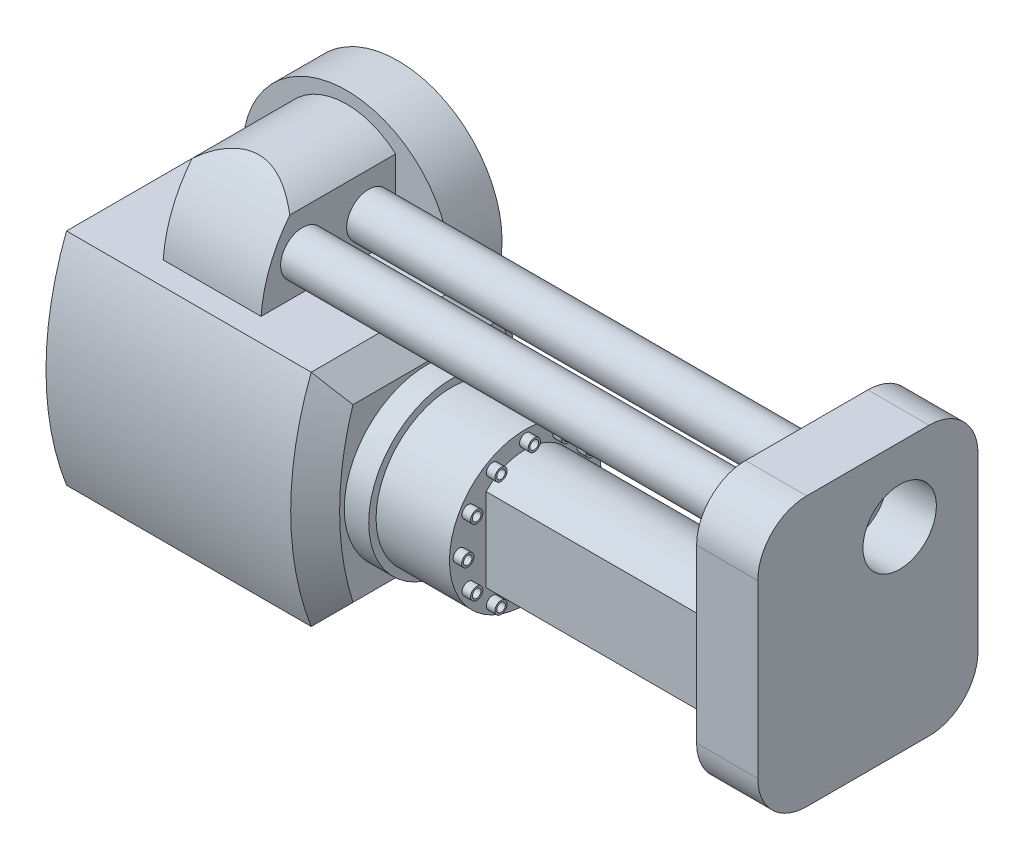
SolidWorks part; units mm, degrees
ref_plane "Front Plane" through (0, 0, 0) normal (0, 0, 1) x (1, 0, 0)
ref_plane "Top Plane" through (0, 0, 0) normal (0, 1, 0) x (1, 0, 0)
ref_plane "Right Plane" through (0, 0, 0) normal (1, 0, 0) x (0, 0, -1)
sketch "Sketch1" plane through (0, 0, 0) normal (1, 0, 0) x (0, 0, -1)
  line L0 (0, 49.4319) -> (0, -79.2344) construction
  line L1 (-101.7614, 0) -> (111.7272, 0) construction
  line L2 (-37.5, 45) -> (37.5, 45)
  line L3 (-37.5, -45) -> (37.5, -45)
  arc A0 (37.5, 45) -> (37.5, -45) centre (-79.119, 0) cw
  arc A1 (-37.5, 45) -> (-37.5, -45) centre (79.119, 0) ccw
  point P7 (0, 45)
  point P13 (0, -45)
  dimension "D3" = 125
  dimension "D1" = 37.5
  dimension "D2" = 37.5
  dimension "D4" = 45
extrude "Boss-Extrude1" add sketch "Sketch1" along normal blind 100
sketch "Sketch2" plane through (100, 0, 0) normal (1, 0, 0) x (0, 0, -1)
  line L2 (37.5, 45) -> (-37.5, 45)
  line L3 (-37.5, -45) -> (37.5, -45)
  line L4 (37.5, 45) -> (-37.5, 45)
  line L5 (-37.5, -45) -> (37.5, -45)
  arc A2 (37.5, -45) -> (37.5, 45) centre (-79.119, 0) ccw
  arc A3 (-37.5, 45) -> (-37.5, -45) centre (79.119, 0) ccw
  arc A4 (37.5, -45) -> (37.5, 45) centre (-79.119, 0) ccw
  arc A5 (-37.5, 45) -> (-37.5, -45) centre (79.119, 0) ccw
  dimension "D1" = 0
extrude "Boss-Extrude2" add sketch "Sketch2" along normal blind 10 draft 45
sketch "Sketch3" plane through (110, 0, 0) normal (1, 0, 0) x (0, 0, -1)
  circle A0 centre (0, 0) radius 34
  dimension "D1" = 68
extrude "Boss-Extrude3" add sketch "Sketch3" along normal blind 10
sketch "Sketch4" plane through (120, 0, 0) normal (1, 0, 0) x (0, 0, -1)
  circle A0 centre (0, 0) radius 31
  dimension "D1" = 62
extrude "Boss-Extrude4" add sketch "Sketch4" along normal blind 30
sketch "Sketch5" plane through (150, 0, 0) normal (1, 0, 0) x (0, 0, -1)
  line L0 (0, 0) -> (27, 0) construction
  circle A0 centre (27, 0) radius 2.5
  circle A1 centre (27, 0) radius 1.75
  circle A2 centre (0, 0) radius 31
  circle A3 centre (0, 0) radius 31
  dimension "D3" = 5
  dimension "D4" = 3.5
  dimension "D2" = 27
  dimension "D1" = 0
extrude "Boss-Extrude5" add sketch "Sketch5" along normal blind 3.5 contours A1 | A0
pattern_circular "CirPattern1" count 12 over 360 about axis through (0, 0, 0.1767) along (1, 0, 0) of "Boss-Extrude5"
sketch "Sketch6" plane through (150, 0, 0) normal (1, 0, 0) x (0, 0, -1)
  line L0 (-17.9184, 0) -> (19.6119, 0) construction
  line L1 (0, -13.9961) -> (0, 16.7727) construction
  line L2 (16, 0) -> (16, 17)
  line L3 (16, 0) -> (16, -17)
  line L4 (-16, 0) -> (-16, 17)
  line L5 (-16, 0) -> (-16, -17)
  arc A2 (-16, 17) -> (16, 17) centre (0, 1.9003) cw
  arc A3 (-16, -17) -> (16, -17) centre (0, -1.9003) ccw
  dimension "D5" = 22
  dimension "D6" = 22
  dimension "D1" = 17
  dimension "D2" = 17
  dimension "D3" = 17
  dimension "D4" = 17
  dimension "D7" = 16
  dimension "D8" = 16
  dimension "D9" = 16
  dimension "D10" = 16
  dimension "D11" = 16
extrude "Boss-Extrude6" add sketch "Sketch6" along normal blind 100
ref_plane "Plane1" through (0, 0, 37.5) normal (0, 0, 1) x (1, 0, 0)
sketch "Sketch10" plane through (0, 0, 37.5) normal (0, 0, 1) x (1, 0, 0)
  line L0 (100, -45) -> (0, -45) construction
  circle A0 centre (50, -45) radius 42.5
  dimension "D1" = 85
extrude "Boss-Extrude10" add sketch "Sketch10" along normal mid plane 21
sketch "Sketch11" plane through (0, 0, 27) normal (0, 0, -1) x (-1, 0, 0)
  line L0 (-50, -45) -> (-70, -45)
  line L1 (-100, -45) -> (0, -45) construction
  line L2 (-70, -45) -> (-70, -75)
  line L3 (-50, -45) -> (-30, -45)
  line L4 (-7.5, -45) -> (-92.5, -45) construction
  line L5 (-30, -45) -> (-30, -75)
  arc A0 (-70, -75) -> (-30, -75) centre (-50, -52.6393) ccw
  dimension "D5" = 30
  dimension "D1" = 20
  dimension "D2" = 20
  dimension "D3" = 30
  dimension "D4" = 30
extrude "Boss-Extrude11" add sketch "Sketch11" along normal blind 30
sketch "Sketch12" plane through (70, 0, 0) normal (1, 0, 0) x (0, 0, -1)
  line L0 (3, -45) -> (3, -87)
  line L1 (3, -45) -> (28, -45)
  line L2 (-37.5, -45) -> (37.5, -45) construction
  arc A0 (28, -45) -> (3, -87) centre (-26.8393, -40.7981) cw
  dimension "D3" = 55
  dimension "D1" = 42
  dimension "D2" = 25
extrude "Boss-Extrude12" add sketch "Sketch12" against normal blind 40
sketch "Sketch13" plane through (0, 0, -3) normal (0, 0, 1) x (1, 0, 0)
  line L3 (30, -75) -> (30, -87)
  line L4 (30, -87) -> (70, -87)
  line L5 (70, -87) -> (70, -75)
  line L6 (30, -75) -> (30, -87)
  line L7 (30, -87) -> (70, -87)
  line L8 (70, -87) -> (70, -75)
  arc A1 (30, -75) -> (70, -75) centre (50, -52.6393) ccw
  arc A2 (30, -75) -> (70, -75) centre (50, -52.6393) ccw
  dimension "D1" = 0
extrude "Cut-Extrude1" cut sketch "Sketch13" against normal blind 40
sketch "Sketch14" plane through (250, 0, 0) normal (1, 0, 0) x (0, 0, -1)
  line L0 (0, 0) -> (-110.3241, 0) construction
  line L2 (-40, 35) -> (10, 35)
  line L3 (-60, 15) -> (-60, -55)
  line L4 (-40, -75) -> (10, -75)
  line L5 (30, 15) -> (30, -55)
  line L6 (-60, 35) -> (30, -75) construction
  line L7 (-60, -75) -> (30, 35) construction
  circle A0 centre (-28, -45) radius 15
  arc A1 (10, -75) -> (30, -55) centre (10, -55) ccw
  arc A2 (30, 15) -> (10, 35) centre (10, 15) ccw
  arc A3 (-40, 35) -> (-60, 15) centre (-40, 15) ccw
  arc A4 (-40, -75) -> (-60, -55) centre (-40, -55) cw
  point P5 (-15, -20)
  point P22 (-54.1421, -69.1421)
  dimension "D1" = 30
  dimension "D8" = 20
  dimension "D9" = 35.5845
  dimension "D2" = 28
  dimension "D3" = 45
  dimension "D4" = 15
  dimension "D5" = 110
  dimension "D6" = 90
  dimension "D7" = 20
extrude "Boss-Extrude13" add sketch "Sketch14" along normal blind 25
sketch "Sketch15" plane through (0, 0, 48) normal (0, 0, 1) x (1, 0, 0)
  circle A0 centre (50, -45) radius 15
  dimension "D1" = 30
extrude "Cut-Extrude2" cut sketch "Sketch15" against normal blind 20
sketch "Sketch16" plane through (70, 0, 0) normal (1, 0, 0) x (0, 0, -1)
  line L0 (-27, -45) -> (-27, -75) construction
  line L1 (28, -45) -> (-27, -45) construction
  circle A0 centre (-16, -59) radius 9
  circle A1 centre (11, -59) radius 9
  dimension "D1" = 18
  dimension "D2" = 18
  dimension "D3" = 11
  dimension "D4" = 27
  dimension "D5" = 14
sketch "Sketch19" plane through (250, 0, 0) normal (-1, 0, 0) x (0, 0, 1)
  circle A0 centre (28, -45) radius 15 construction
  circle A1 centre (28, -45) radius 15
extrude "Boss-Extrude15" add sketch "Sketch19" against normal blind 5
extrude "Boss-Extrude16" add sketch "Sketch16" along normal up to surface (180 mm away) up to face at (250, 0, 0)
sketch "Sketch21" plane through (0, 0, 28) normal (0, 0, 1) x (1, 0, 0)
  point P0 (50, -45)
  point P1 (0, 0)
move or copy body "Body-Move/Copy1" bodies to move or copy 119 copy no translate (-50, 45, -28)
move or copy body "Body-Move/Copy2" bodies to move or copy 120 copy no rotation origin (0, 0, 0) rotation axis (0, 1, 0) rotation angle 180
move or copy body "Body-Move/Copy3" bodies to move or copy 121 copy no rotation origin (0, 0, 0) rotation axis (0, 0, 1) rotation angle 180
equation "\"3..00mm\"=30"
